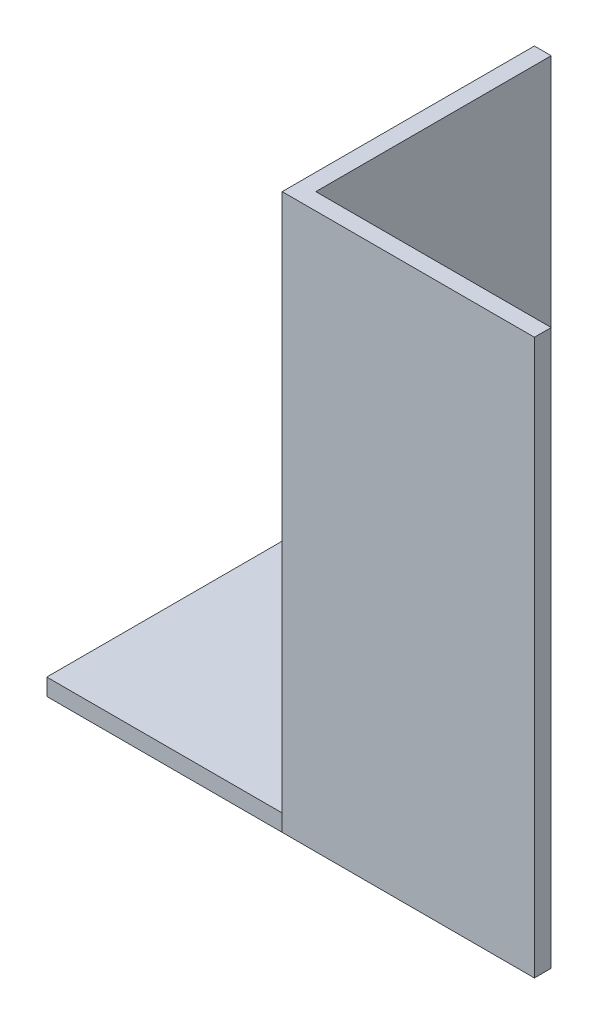
SolidWorks part; units mm, degrees
material "1060 Сплав"
ref_plane "Спереди" through (0, 0, 0) normal (0, 0, 1) x (1, 0, 0)
ref_plane "Сверху" through (0, 0, 0) normal (0, 1, 0) x (1, 0, 0)
ref_plane "Справа" through (0, 0, 0) normal (1, 0, 0) x (0, 0, -1)
sketch "Эскиз1" plane through (0, 0, 0) normal (0, 1, 0) x (1, 0, 0)
  line L0 (0, 0) -> (0, 15)
  line L1 (0, 15) -> (1, 15)
  line L2 (1, 15) -> (1, 1)
  line L3 (1, 1) -> (15, 1)
  line L4 (15, 1) -> (15, 0)
  line L5 (15, 0) -> (0, 0)
  dimension "D1" = 1
  dimension "D2" = 15
extrude "Бобышка-Вытянуть1" add sketch "Эскиз1" along normal blind 53
sketch "Эскиз3" plane through (0, 0, 0) normal (0, -1, 0) x (1, 0, 0)
  line L6 (15, 0) -> (0, 0)
  line L7 (0, 0) -> (0, -15)
  line L8 (0, -15) -> (1, -15)
  line L9 (1, -15) -> (1, -1)
  line L10 (1, -1) -> (15, -1)
  line L11 (15, -1) -> (15, 0)
  line L12 (15, 0) -> (0, 0)
  line L13 (0, 0) -> (0, -15)
  line L14 (0, -15) -> (1, -15)
  line L15 (1, -15) -> (1, -1)
  line L16 (1, -1) -> (15, -1)
  line L17 (15, -1) -> (15, 0)
  dimension "D1" = 0
extrude "Вырез-Вытянуть2" cut sketch "Эскиз3" against normal blind 20
sketch "Эскиз5" plane through (1, 0, 0) normal (1, 0, 0) x (0, 0, -1)
  line L0 (1, 20) -> (15, 20)
  line L1 (1, 20) -> (1, 19)
  line L2 (15, 20) -> (15, 19)
  line L3 (1, 19) -> (15, 19)
  line L5 (15, 20) -> (1, 20) construction
  dimension "D1" = 1
extrude "Бобышка-Вытянуть2" add sketch "Эскиз5" against normal blind 16
